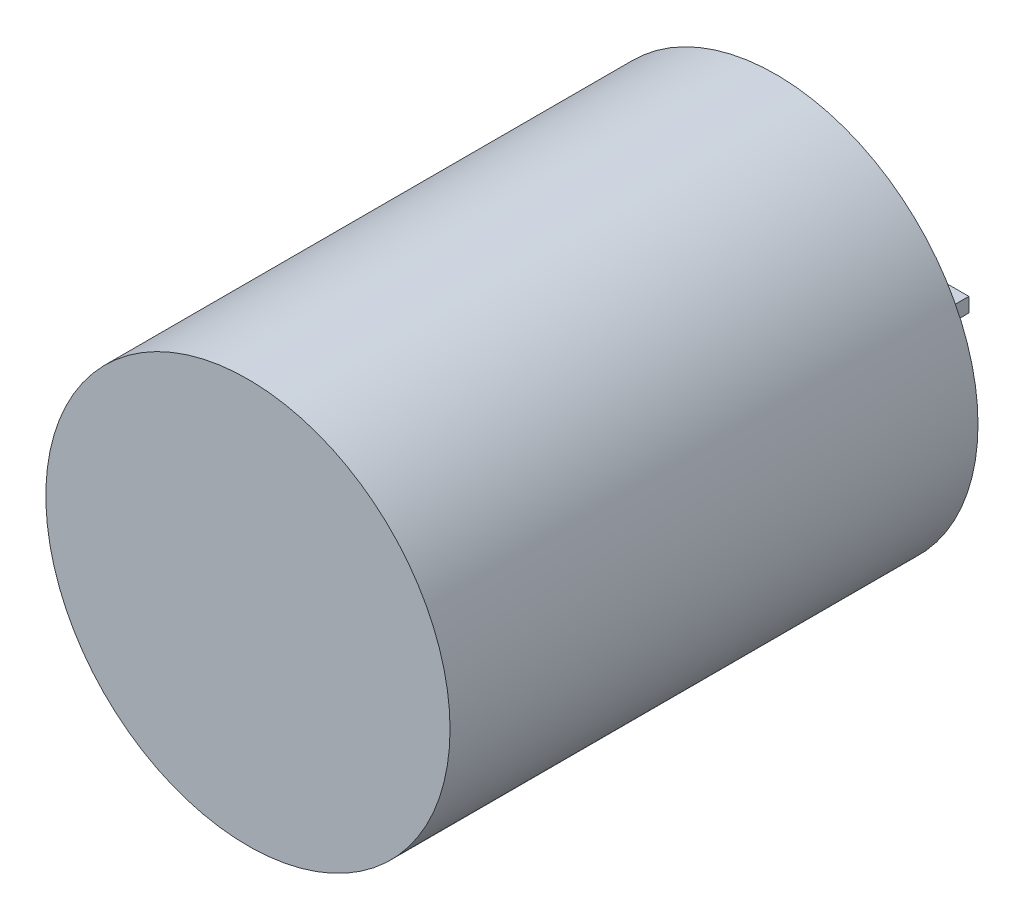
SolidWorks part; units mm, degrees
ref_plane "Front Plane" through (0, 0, 0) normal (0, 0, 1) x (1, 0, 0)
ref_plane "Top Plane" through (0, 0, 0) normal (0, 1, 0) x (1, 0, 0)
ref_plane "Right Plane" through (0, 0, 0) normal (1, 0, 0) x (0, 0, -1)
sketch "Sketch1" plane through (0, 0, 0) normal (0, 0, 1) x (1, 0, 0)
  circle A0 centre (0, 0) radius 12.446
  dimension "D1" = 24.892
extrude "Boss-Extrude1" add sketch "Sketch1" along normal blind 32.512
sketch "Sketch2" plane through (0, 0, 0) normal (0, 0, 1) x (1, 0, 0)
  line L0 (0, 0) -> (12.446, 0) construction
  line L1 (-5.7826, -0.4445) -> (-4.2174, -0.4445)
  line L2 (-5.7826, -0.4445) -> (-5.7826, 0.4445)
  line L3 (-5.7826, 0.4445) -> (-4.2174, 0.4445)
  line L4 (-4.2174, -0.4445) -> (-4.2174, 0.4445)
  line L5 (4.2174, 0.4445) -> (5.7826, 0.4445)
  line L6 (4.2174, 0.4445) -> (4.2174, -0.4445)
  line L7 (4.2174, -0.4445) -> (5.7826, -0.4445)
  line L8 (5.7826, 0.4445) -> (5.7826, -0.4445)
  line L9 (12.446, 0) -> (-12.446, 0) construction
  circle A0 centre (0, 0) radius 12.446 construction
  circle A1 centre (-5, 0) radius 0.9 construction
  circle A2 centre (5, 0) radius 0.9 construction
  point P19 (5.7971, -0.6038)
  point P20 (4.4452, 0.832)
  point P21 (-4.2263, -0.6336)
  point P22 (-5.6284, 0.7779)
  point P23 (0, 0)
  point P24 (-5.6899, -0.7239)
  point P25 (4.2866, -0.7008)
  dimension "D3" = 1.8
  dimension "D4" = 1.8
  dimension "D1" = 5
  dimension "D2" = 5
  dimension "D5" = 0.889
extrude "Boss-Extrude2" add sketch "Sketch2" against normal blind 6.1
